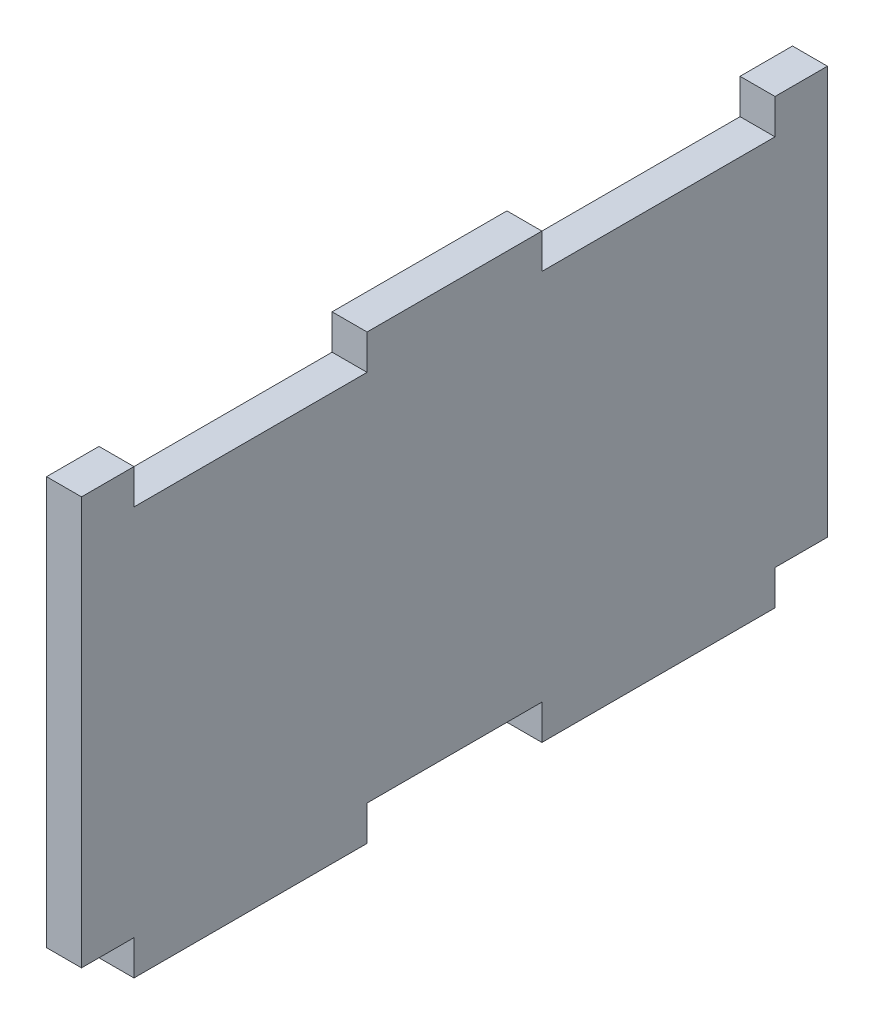
SolidWorks part; units mm, degrees
ref_plane "Front Plane" through (0, 0, 0) normal (0, 0, 1) x (1, 0, 0)
ref_plane "Top Plane" through (0, 0, 0) normal (0, 1, 0) x (1, 0, 0)
ref_plane "Right Plane" through (0, 0, 0) normal (1, 0, 0) x (0, 0, -1)
sketch "Sketch1" plane through (0, 0, 0) normal (1, 0, 0) x (0, 0, -1)
  line L0 (24.5, 0) -> (39.5, 0)
  line L1 (0, 0) -> (4.5, 0)
  line L2 (0, 0) -> (0, 35)
  line L3 (0, 35) -> (4.5, 35)
  line L4 (277, 0) -> (277, 35)
  line L5 (24.5, 35) -> (39.5, 35)
  line L6 (39.5, 32) -> (59.5, 32)
  line L7 (39.5, 0) -> (39.5, -3)
  line L8 (4.5, 0) -> (4.5, -3)
  line L9 (4.5, -3) -> (24.5, -3)
  line L10 (24.5, 0) -> (24.5, -3)
  line L11 (4.5, 35) -> (4.5, 32)
  line L12 (4.5, 32) -> (24.5, 32)
  line L13 (39.5, -3) -> (59.5, -3)
  line L14 (59.5, 0) -> (59.5, -3)
  line L15 (74.5, 0) -> (74.5, -3)
  line L16 (74.5, -3) -> (94.5, -3)
  line L17 (94.5, 0) -> (94.5, -3)
  line L18 (109.5, 0) -> (109.5, -3)
  line L19 (109.5, -3) -> (129.5, -3)
  line L20 (129.5, 0) -> (129.5, -3)
  line L21 (144.5, 0) -> (144.5, -3)
  line L22 (144.5, -3) -> (164.5, -3)
  line L23 (164.5, 0) -> (164.5, -3)
  line L24 (179.5, 0) -> (179.5, -3)
  line L25 (179.5, -3) -> (199.5, -3)
  line L26 (199.5, 0) -> (199.5, -3)
  line L27 (214.5, 0) -> (214.5, -3)
  line L28 (214.5, -3) -> (234.5, -3)
  line L29 (234.5, 0) -> (234.5, -3)
  line L30 (249.5, 0) -> (249.5, -3)
  line L31 (249.5, -3) -> (269.5, -3)
  line L32 (269.5, 0) -> (269.5, -3)
  line L33 (59.5, 0) -> (74.5, 0)
  line L34 (94.5, 0) -> (109.5, 0)
  line L35 (129.5, 0) -> (144.5, 0)
  line L36 (164.5, 0) -> (179.5, 0)
  line L37 (199.5, 0) -> (214.5, 0)
  line L38 (234.5, 0) -> (249.5, 0)
  line L39 (269.5, 0) -> (277, 0)
  line L40 (24.5, 35) -> (24.5, 32)
  line L41 (59.5, 35) -> (59.5, 32)
  line L42 (39.5, 35) -> (39.5, 32)
  line L43 (74.5, 32) -> (94.5, 32)
  line L44 (94.5, 35) -> (94.5, 32)
  line L45 (74.5, 35) -> (74.5, 32)
  line L46 (109.5, 32) -> (129.5, 32)
  line L47 (129.5, 35) -> (129.5, 32)
  line L48 (109.5, 35) -> (109.5, 32)
  line L49 (144.5, 32) -> (164.5, 32)
  line L50 (164.5, 35) -> (164.5, 32)
  line L51 (144.5, 35) -> (144.5, 32)
  line L52 (179.5, 32) -> (199.5, 32)
  line L53 (199.5, 35) -> (199.5, 32)
  line L54 (179.5, 35) -> (179.5, 32)
  line L55 (214.5, 32) -> (234.5, 32)
  line L56 (234.5, 35) -> (234.5, 32)
  line L57 (214.5, 35) -> (214.5, 32)
  line L58 (249.5, 32) -> (269.5, 32)
  line L59 (269.5, 35) -> (269.5, 32)
  line L60 (249.5, 35) -> (249.5, 32)
  line L61 (59.5, 35) -> (74.5, 35)
  line L62 (94.5, 35) -> (109.5, 35)
  line L63 (129.5, 35) -> (144.5, 35)
  line L64 (164.5, 35) -> (179.5, 35)
  line L65 (269.5, 35) -> (277, 35)
  line L66 (199.5, 35) -> (214.5, 35)
  line L67 (234.5, 35) -> (249.5, 35)
  dimension "D1" = 20
  dimension "D2" = 4.5
  dimension "D3" = 277
  dimension "D4" = 3
  dimension "D6" = 35
  dimension "D7" = 15
  dimension "D5" = 8
  dimension "D8" = 8
extrude "Boss-Extrude1" add sketch "Sketch1" along normal blind 3 contours L3 L11 L12 L40 L5 L42 L6 L41 L61 L45 L43 L44 L62 L48 L46 L47 L63 L51 L49 L50 L64 L54 L52 L53 L66 L57 L55 L56 L67 L60 L58 L59 L65 L4 L39 L32 L31 L30 L38 L29 L28 L27 L37 L26 L25 L24 L36 L23 L22 L21 L35 L20 L19 L18 L34 L17 L16 L15 L33 L14 L13 L7 L0 L10 L9 L8 L1 L2
sketch "Sketch2" plane through (3, 0, 0) normal (1, 0, 0) x (0, 0, -1)
  line L0 (0, 0) -> (0, 35) construction
  line L1 (64, 40) -> (277, 40)
  line L2 (64, 40) -> (64, -5)
  line L3 (64, -5) -> (277, -5)
  line L4 (277, 40) -> (277, -5)
  line L5 (64, 40) -> (277, -5) construction
  line L6 (64, -5) -> (277, 40) construction
  line L7 (277, 0) -> (277, 35) construction
  point P4 (170.5, 17.5)
  point P7 (64, 17.5)
  point P8 (0, 17.5)
  point P11 (277, 17.5)
  dimension "D1" = 64
  dimension "D2" = 45
extrude "Cut-Extrude1" cut sketch "Sketch2" against normal blind 10
